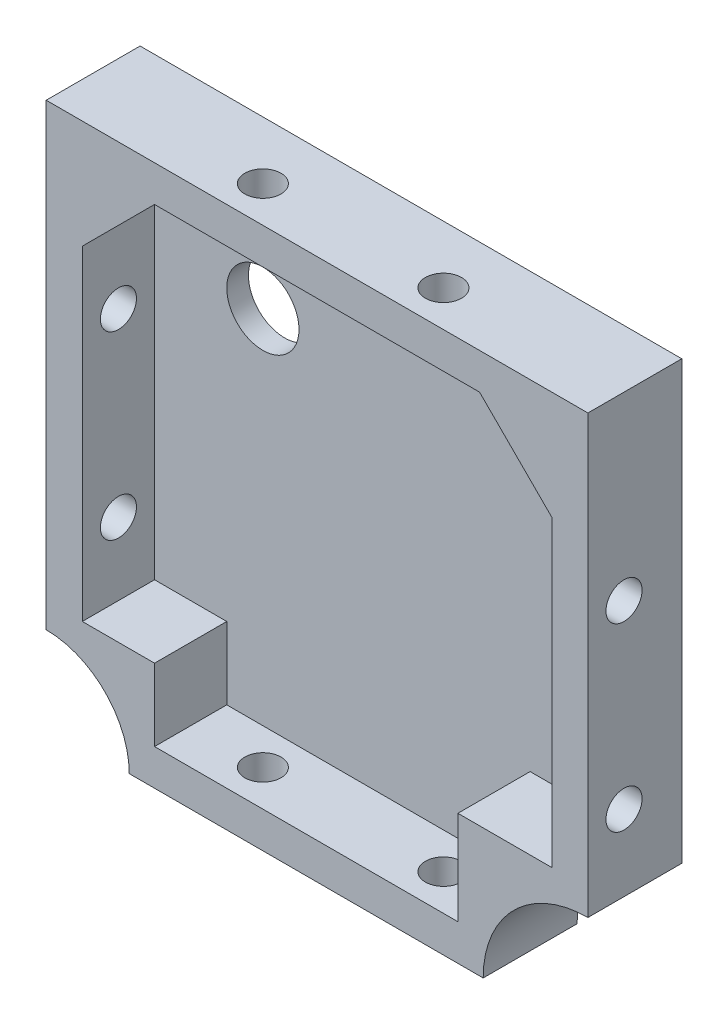
SolidWorks part; units mm, degrees
ref_plane "Plan de face" through (0, 0, 0) normal (0, 0, 1) x (1, 0, 0)
ref_plane "Plan de dessus" through (0, 0, 0) normal (0, 1, 0) x (1, 0, 0)
ref_plane "Plan de droite" through (0, 0, 0) normal (1, 0, 0) x (0, 0, -1)
sketch "Esquisse1" plane through (0, 0, 0) normal (0, 0, 1) x (1, 0, 0)
  line L0 (44.1184, 33.7284) -> (54.1184, 33.7284)
  line L1 (-20.8816, 33.7284) -> (44.1184, 33.7284)
  line L2 (-20.8816, 33.7284) -> (-20.8816, -41.2716)
  line L3 (-20.8816, -41.2716) -> (54.1184, -41.2716)
  line L4 (54.1184, 23.7284) -> (54.1184, -41.2716)
  line L5 (54.1184, 33.7284) -> (54.1184, 23.7284)
  point P6 (54.1184, 33.7284)
  dimension "D1" = 75
  dimension "D2" = 75
extrude "Boss.-Extru.1" add sketch "Esquisse1" along normal blind 13
shell "Coque1" thickness 5
sketch "Esquisse2" plane through (-20.8816, 0, 0) normal (-1, 0, 0) x (0, 0, 1)
  line L0 (13, 33.7284) -> (13, -41.2716) construction
  line L1 (13, 33.7284) -> (0, 33.7284) construction
  line L2 (13, -41.2716) -> (0, -41.2716) construction
  circle A0 centre (8, 8.7284) radius 2.5
  circle A1 centre (8, -16.2716) radius 2.5
  dimension "D1" = 5
  dimension "D2" = 5
  dimension "D3" = 5
  dimension "D4" = 5
  dimension "D5" = 25
  dimension "D6" = 25
extrude "Enlèv. mat.-Extru.1" cut sketch "Esquisse2" against normal up to surface (75 mm away) contours A1 | A0 up to face at (54.1184, -3.7716, 6.5)
sketch "Esquisse3" plane through (0, -41.2716, 0) normal (0, -1, 0) x (1, 0, 0)
  line L0 (-20.8816, 13) -> (54.1184, 13) construction
  line L2 (54.1184, 13) -> (54.1184, 0) construction
  line L3 (-20.8816, 13) -> (-20.8816, 0) construction
  circle A0 centre (4.1184, 8) radius 2.5
  circle A1 centre (29.1184, 8) radius 2.5
  dimension "D1" = 5
  dimension "D2" = 5
  dimension "D3" = 5
  dimension "D4" = 5
  dimension "D5" = 25
  dimension "D6" = 25
extrude "Enlèv. mat.-Extru.2" cut sketch "Esquisse3" against normal up to surface (75 mm away) up to face at (16.6184, 33.7284, 6.5)
sketch "Esquisse4" plane through (0, 0, 3) normal (0, 0, 1) x (1, 0, 0)
  line L0 (-5.8816, 28.7284) -> (-15.8816, 18.7284)
  line L1 (49.1184, 28.7284) -> (-15.8816, 28.7284) construction
  line L2 (-15.8816, 28.7284) -> (-15.8816, -36.2716) construction
  line L3 (-15.8816, 18.7284) -> (-15.8816, 28.7284)
  line L4 (-15.8816, 28.7284) -> (-5.8816, 28.7284)
  line L5 (49.1184, 28.7284) -> (49.1184, 18.7284)
  line L6 (49.1184, -36.2716) -> (49.1184, 28.7284) construction
  line L7 (49.1184, 18.7284) -> (39.1184, 28.7284)
  line L8 (39.1184, 28.7284) -> (49.1184, 28.7284)
  line L9 (49.1184, 28.7284) -> (-15.8816, 28.7284) construction
  line L11 (54.1184, -41.2716) -> (36.1184, -41.2716)
  line L13 (54.1184, -41.2716) -> (54.1184, -23.2716)
  line L14 (-20.8816, -26.2716) -> (-5.8816, -26.2716)
  line L15 (-20.8816, -41.2716) -> (54.1184, -41.2716) construction
  line L16 (-5.8816, -26.2716) -> (-5.8816, -41.2716)
  line L17 (-5.8816, -41.2716) -> (-20.8816, -41.2716)
  line L18 (-20.8816, -41.2716) -> (-20.8816, -26.2716)
  line L19 (-20.8816, 33.7284) -> (-20.8816, -41.2716) construction
  line L20 (54.1184, -23.2716) -> (36.1184, -23.2716)
  line L21 (36.1184, -41.2716) -> (36.1184, -23.2716)
  dimension "D1" = 10
  dimension "D2" = 10
  dimension "D3" = 10
  dimension "D4" = 10
  dimension "D5" = 18
  dimension "D6" = 18
  dimension "D7" = 15
  dimension "D8" = 15
  dimension "D9" = 0
  dimension "D10" = 0
extrude "Boss.-Extru.2" add sketch "Esquisse4" along normal up to surface (10 mm away) up to face at (16.6184, -3.7716, 13)
sketch "Esquisse5" plane through (0, 0, 13) normal (0, 0, 1) x (1, 0, 0)
  circle A0 centre (-20.8816, -41.2716) radius 11.5
  circle A1 centre (54.1184, -41.2716) radius 14.5
  dimension "D1" = 23
  dimension "D2" = 29
extrude "Enlèv. mat.-Extru.3" cut sketch "Esquisse5" against normal up to surface (13 mm away) up to face at (16.6184, -3.7716, 0)
sketch "Esquisse6" plane through (0, 0, 3) normal (0, 0, 1) x (1, 0, 0)
  line L0 (54.1184, 33.7284) -> (-20.8816, 33.7284) construction
  line L1 (-20.8816, 33.7284) -> (-20.8816, -29.7716) construction
  circle A0 centre (-0.8816, 13.7284) radius 5
  dimension "D3" = 10
  dimension "D1" = 20
  dimension "D2" = 20
extrude "Enlèv. mat.-Extru.4" cut sketch "Esquisse6" against normal up to surface (3 mm away) contours A0 up to face at (16.0149, -11.0408, 0)
